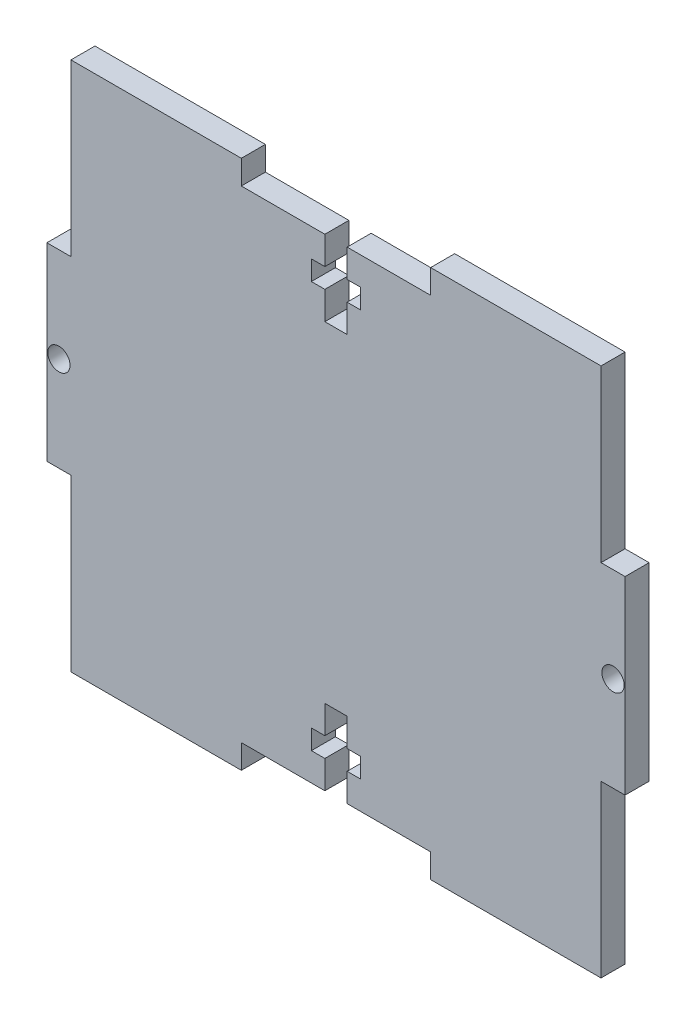
SolidWorks part; units mm, degrees
ref_plane "Front Plane" through (0, 0, 0) normal (0, 0, 1) x (1, 0, 0)
ref_plane "Top Plane" through (0, 0, 0) normal (0, 1, 0) x (1, 0, 0)
ref_plane "Right Plane" through (0, 0, 0) normal (1, 0, 0) x (0, 0, -1)
sketch "Sketch1" plane through (0, 0, 0) normal (0, 0, 1) x (1, 0, 0)
  line L0 (0, 35) -> (0, -35) construction
  line L1 (-35, 35) -> (35, 35)
  line L2 (-35, 35) -> (-35, -35)
  line L3 (-35, -35) -> (35, -35)
  line L4 (35, 35) -> (35, -35)
  line L5 (-35, 35) -> (35, -35) construction
  line L6 (-35, -35) -> (35, 35) construction
  line L7 (-35, 0) -> (35, 0) construction
  line L8 (-3.25, -25.525) -> (3.25, -25.525)
  line L9 (12.5, 35) -> (-12.5, 35)
  line L10 (12.5, 35) -> (12.5, 31.825)
  line L11 (12.5, 31.825) -> (-12.5, 31.825)
  line L12 (-12.5, 35) -> (-12.5, 31.825)
  line L13 (12.5, 35) -> (-12.5, 31.825) construction
  line L14 (12.5, 31.825) -> (-12.5, 35) construction
  line L15 (-1.47, 31.825) -> (1.47, 31.825)
  line L16 (-1.47, 31.825) -> (-1.47, 21.825)
  line L17 (-1.47, 21.825) -> (1.47, 21.825)
  line L18 (1.47, 31.825) -> (1.47, 21.825)
  line L19 (-1.47, 31.825) -> (1.47, 21.825) construction
  line L20 (-1.47, 21.825) -> (1.47, 31.825) construction
  line L21 (-3.25, 28.125) -> (3.25, 28.125)
  line L22 (-3.25, 28.125) -> (-3.25, 25.525)
  line L23 (-3.25, 25.525) -> (3.25, 25.525)
  line L24 (3.25, 28.125) -> (3.25, 25.525)
  line L25 (-3.25, 28.125) -> (3.25, 25.525) construction
  line L26 (-3.25, 25.525) -> (3.25, 28.125) construction
  line L27 (3.25, -28.125) -> (3.25, -25.525)
  line L28 (-3.25, -28.125) -> (3.25, -28.125)
  line L29 (-3.25, -28.125) -> (-3.25, -25.525)
  line L30 (-1.47, -21.825) -> (1.47, -21.825)
  line L31 (1.47, -31.825) -> (1.47, -21.825)
  line L32 (-1.47, -31.825) -> (1.47, -31.825)
  line L33 (-1.47, -31.825) -> (-1.47, -21.825)
  line L34 (12.5, -31.825) -> (-12.5, -31.825)
  line L35 (-12.5, -35) -> (-12.5, -31.825)
  line L36 (12.5, -35) -> (-12.5, -35)
  line L37 (12.5, -35) -> (12.5, -31.825)
  line L38 (38.175, -12.5) -> (35, -12.5)
  line L39 (-38.175, 12.5) -> (-35, 12.5)
  line L40 (-38.175, 12.5) -> (-38.175, -12.5)
  line L41 (-38.175, -12.5) -> (-35, -12.5)
  line L42 (-35, 12.5) -> (-35, -12.5)
  line L43 (-38.175, 12.5) -> (-35, -12.5) construction
  line L44 (-38.175, -12.5) -> (-35, 12.5) construction
  line L45 (35, 12.5) -> (35, -12.5)
  line L46 (38.175, 12.5) -> (35, 12.5)
  line L47 (38.175, 12.5) -> (38.175, -12.5)
  circle A0 centre (-36.5875, 0) radius 1.47
  circle A1 centre (36.5875, 0) radius 1.47
  point P0 (0, 0)
  point P10 (0, 33.4125)
  point P15 (0, 26.825)
  point P20 (0, 26.825)
  point P37 (-36.5875, 0)
  dimension "D11" = 2.94
  dimension "D1" = 70
  dimension "D2" = 70
  dimension "D3" = 3.175
  dimension "D4" = 10
  dimension "D5" = 2.94
  dimension "D6" = 25
  dimension "D7" = 6.5
  dimension "D8" = 2.6
  dimension "D9" = 6.3
  dimension "D10" = 3.175
extrude "Boss-Extrude1" add sketch "Sketch1" along normal mid plane 3.175 contours L21 L24 L23 L18 L17 L16 L22 L11 L12 L1 L2 L3 L4 L10 | L40 L39 L42 L41 | A0 | L38 L45 L46 L47 | A1
